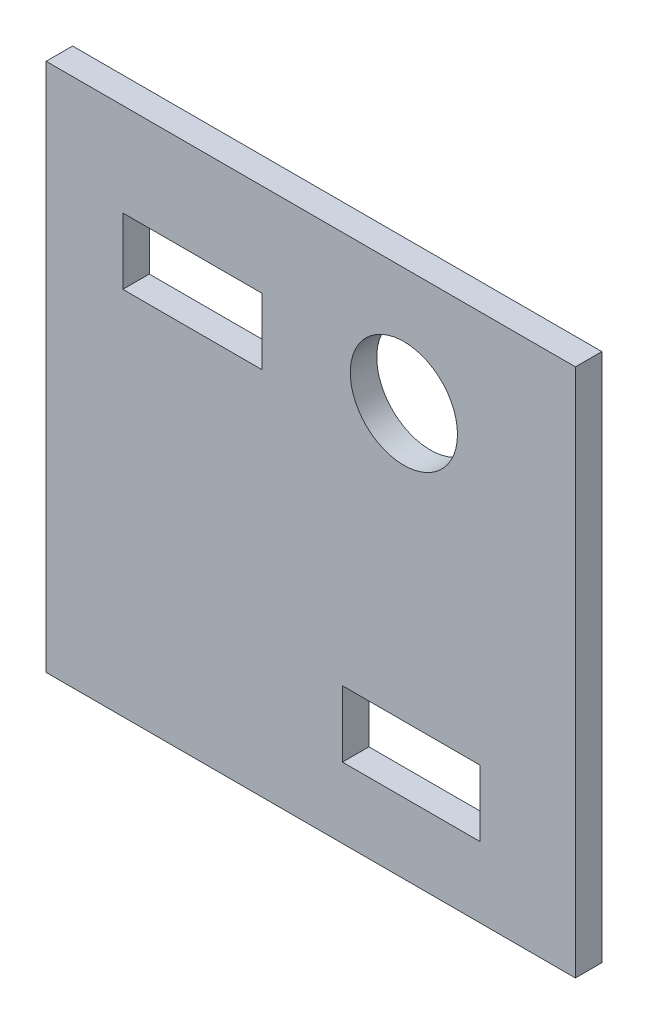
SolidWorks part; units mm, degrees
ref_plane "Front Plane" through (0, 0, 0) normal (0, 0, 1) x (1, 0, 0)
ref_plane "Top Plane" through (0, 0, 0) normal (0, 1, 0) x (1, 0, 0)
ref_plane "Right Plane" through (0, 0, 0) normal (1, 0, 0) x (0, 0, -1)
sketch "Sketch1" plane through (0, 0, 0) normal (0, 0, 1) x (1, 0, 0)
  line L1 (-17.3953, 14.6512) -> (22.6047, 14.6512)
  line L2 (-17.3953, 14.6512) -> (-17.3953, -25.3488)
  line L3 (-17.3953, -25.3488) -> (22.6047, -25.3488)
  line L4 (22.6047, 14.6512) -> (22.6047, -25.3488)
  dimension "D1" = 40
  dimension "D2" = 40
extrude "Boss-Extrude1" add sketch "Sketch1" along normal blind 2
sketch "Sketch2" plane through (0, 0, 2) normal (0, 0, 1) x (1, 0, 0)
  line L1 (-11.5996, 7.6222) -> (-1.0996, 7.6222)
  line L2 (-11.5996, 7.6222) -> (-11.5996, 2.6222)
  line L3 (-11.5996, 2.6222) -> (-1.0996, 2.6222)
  line L4 (-1.0996, 7.6222) -> (-1.0996, 2.6222)
  line L5 (4.9986, -15.0222) -> (15.3986, -15.0222)
  line L6 (4.9986, -15.0222) -> (4.9986, -20.0222)
  line L7 (4.9986, -20.0222) -> (15.3986, -20.0222)
  line L8 (15.3986, -15.0222) -> (15.3986, -20.0222)
  circle A0 centre (9.6409, 5.775) radius 4.0512
  dimension "D1" = 10.5
  dimension "D2" = 10.4
  dimension "D3" = 5
  dimension "D4" = 5
extrude "Cut-Extrude1" cut sketch "Sketch2" against normal blind 2
